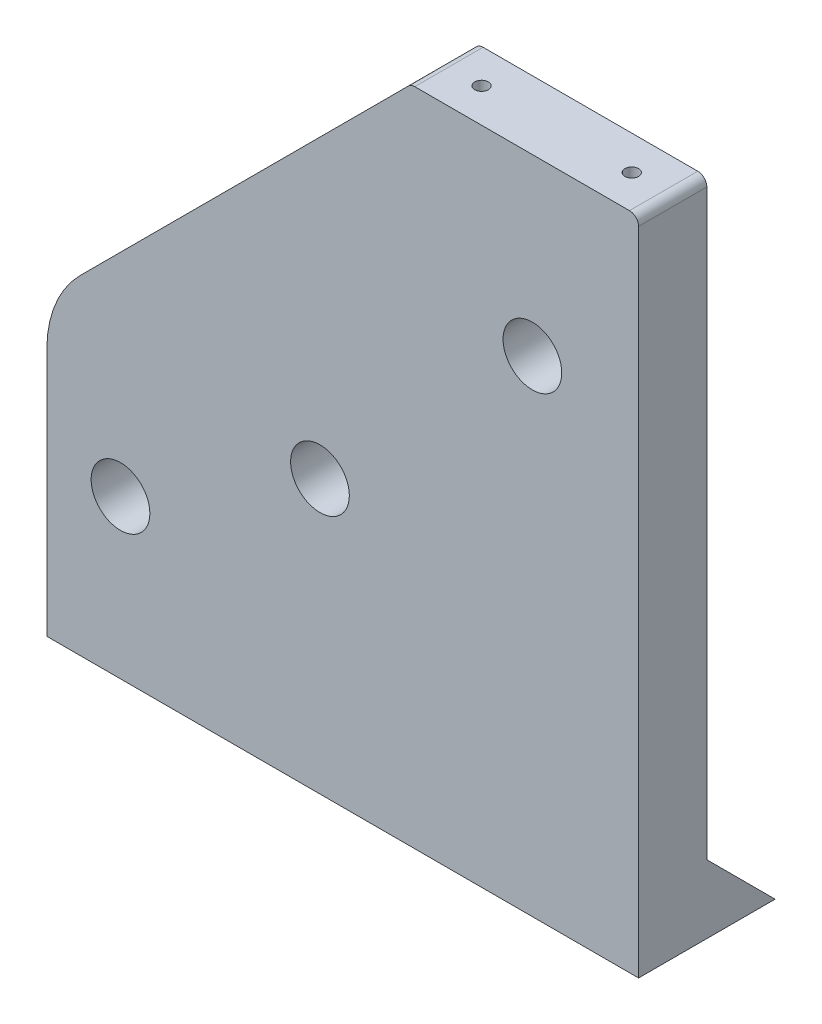
SolidWorks part; units mm, degrees
ref_plane "Front Plane" through (0, 0, 0) normal (0, 0, 1) x (1, 0, 0)
ref_plane "Top Plane" through (0, 0, 0) normal (0, 1, 0) x (1, 0, 0)
ref_plane "Right Plane" through (0, 0, 0) normal (1, 0, 0) x (0, 0, -1)
sketch "Sketch1" plane through (0, 0, 0) normal (0, 0, 1) x (1, 0, 0)
  line L0 (60, 60) -> (106.669, 106.669) construction
  line L1 (0, 0) -> (130, 0)
  line L2 (0, 0) -> (0, 145)
  line L3 (0, 145) -> (130, 145)
  line L4 (130, 0) -> (130, 145)
  line L5 (16.1791, 34.7) -> (60, 60) construction
  circle A0 centre (60, 60) radius 6.45
  circle A1 centre (106.669, 106.669) radius 6.45
  circle A2 centre (16.1791, 34.7) radius 6.45
  dimension "D4" = 12.9
  dimension "D1" = 130
  dimension "D2" = 145
  dimension "D3" = 66
  dimension "D5" = 60
  dimension "D6" = 45
  dimension "D7" = 70
  dimension "D8" = 50.6
  dimension "D9" = 30
extrude "Boss-Extrude1" add sketch "Sketch1" along normal blind 15
chamfer "Chamfer1" distance 80 angle 45 1 edges at (0, 145, 7.5)
fillet "Fillet2" radius 25 1 edges at (0, 65, 7.5)
fillet "Fillet1" radius 2 2 edges at (130, 145, 7.5) (80, 145, 7.5)
sketch "Sketch2" plane through (130, 0, 0) normal (1, 0, 0) x (0, 0, -1)
  line L0 (0, 15) -> (15, 0)
  line L1 (0, 0) -> (0, 143) construction
  line L2 (15, 0) -> (0, 0)
  line L3 (0, 0) -> (0, 15)
  point P4 (10.4336, 1.1133)
  dimension "D1" = 15
extrude "Boss-Extrude2" add sketch "Sketch2" against normal through all
sketch "Sketch3" plane through (0, 0, 0) normal (0, -1, 0) x (1, 0, 0)
  line L0 (0, 15) -> (130, 15) construction
  line L1 (0, 15) -> (0, -15) construction
  circle A0 centre (35, 7.5) radius 2.75
  circle A1 centre (105, 7.5) radius 2.75
  point P6 (0, 0)
  dimension "D1" = 7.5
  dimension "D3" = 35
  dimension "D4" = 5.5
  dimension "D2" = 70
extrude "Cut-Extrude1" cut sketch "Sketch3" against normal blind 45
sketch "Sketch4" plane through (0, 145, 0) normal (0, 1, 0) x (1, 0, 0)
  line L0 (128, -15) -> (80.8284, -15) construction
  line L1 (130, 0) -> (130, -15) construction
  circle A0 centre (121, -7.5) radius 1.5
  circle A1 centre (88, -7.5) radius 1.5
  point P4 (0, 0)
  point P5 (121.9629, -8.958)
  point P8 (0, 0)
  dimension "D2" = 33
  dimension "D3" = 9
  dimension "D4" = 3
  dimension "D1" = 7.5
extrude "Cut-Extrude2" cut sketch "Sketch4" against normal blind 25
sketch "Sketch5" plane through (0, 0, 0) normal (0, 0, -1) x (-1, 0, 0)
  circle A0 centre (-106.669, 106.669) radius 15.7783
extrude "Cut-Extrude3" [suppressed] cut sketch "Sketch5" against normal blind 25 flip side to cut
sketch "Sketch6" plane through (0, 0, 0) normal (0, -1, 0) x (1, 0, 0)
  line L0 (0, 15) -> (130, 15) construction
  line L1 (42.4891, 0) -> (27.5109, 0)
  line L2 (42.4891, 0) -> (42.4891, 15)
  line L3 (42.4891, 15) -> (27.5109, 15)
  line L4 (27.5109, 0) -> (27.5109, 15)
  line L5 (42.4891, 0) -> (27.5109, 15) construction
  line L6 (42.4891, 15) -> (27.5109, 0) construction
  point P0 (35, 7.5)
extrude "Cut-Extrude5" [suppressed] cut sketch "Sketch6" against normal through all both and the other way through all flip side to cut
sketch "Sketch7" [suppressed] plane through (0, 0, 15) normal (0, 0, 1) x (1, 0, 0)
  line L0 (27.5109, 92.5109) -> (27.5109, 0) construction
  line L1 (27.5109, 17.1904) -> (42.4891, 17.1904)
  line L2 (27.5109, 17.1904) -> (27.5109, 107.4891)
  line L3 (27.5109, 107.4891) -> (42.4891, 107.4891)
  line L4 (42.4891, 17.1904) -> (42.4891, 107.4891)
extrude "Cut-Extrude6" [suppressed] cut sketch "Sketch7" against normal through all both and the other way through all
sketch "Sketch8" plane through (0, 0, 15) normal (0, 0, 1) x (1, 0, 0)
  line L0 (128, 145) -> (80.8284, 145) construction
  line L1 (114.2648, 145) -> (130, 145)
  line L2 (114.2648, 145) -> (114.2648, 132.7474)
  line L3 (114.2648, 132.7474) -> (130, 132.7474)
  line L4 (130, 145) -> (130, 132.7474)
  line L5 (130, 0) -> (130, 143) construction
  point P8 (114.2648, 145)
  point P9 (0, 0)
extrude "Cut-Extrude7" [suppressed] cut sketch "Sketch8" against normal through all both and the other way through all flip side to cut
